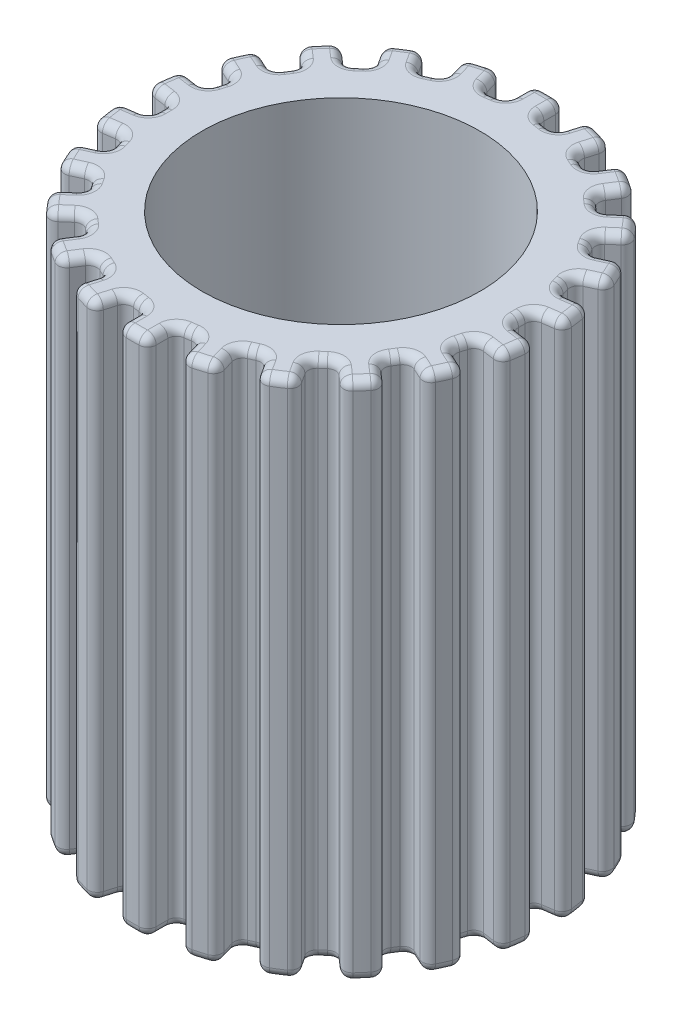
SolidWorks part; units mm, degrees
ref_plane "Front Plane" through (0, 0, 0) normal (0, 0, 1) x (1, 0, 0)
ref_plane "Top Plane" through (0, 0, 0) normal (0, 1, 0) x (1, 0, 0)
ref_plane "Right Plane" through (0, 0, 0) normal (1, 0, 0) x (0, 0, -1)
sketch "Sketch2" plane through (0, 0, 0) normal (0, 1, 0) x (1, 0, 0)
  line L0 (0, 4) -> (0, 6) construction
  line L1 (0.428, 5.9847) -> (0.428, 5.1882)
  line L2 (-0.428, 5.9847) -> (-0.428, 5.1882)
  line L3 (2.0968, 5.6217) -> (1.8724, 4.8575)
  line L4 (1.2754, 5.8629) -> (1.051, 5.0987)
  line L5 (3.5957, 4.8032) -> (3.1651, 4.1332)
  line L6 (2.8755, 5.2661) -> (2.4449, 4.596)
  line L7 (4.8032, 3.5957) -> (4.2013, 3.0741)
  line L8 (4.2426, 4.2426) -> (3.6407, 3.7211)
  line L9 (5.6217, 2.0968) -> (4.8972, 1.7659)
  line L10 (5.2661, 2.8755) -> (4.5416, 2.5446)
  line L11 (5.9847, 0.428) -> (5.1963, 0.3147)
  line L12 (5.8629, 1.2754) -> (5.0745, 1.162)
  line L13 (5.8629, -1.2754) -> (5.0745, -1.162)
  line L14 (5.9847, -0.428) -> (5.1963, -0.3147)
  line L15 (5.2661, -2.8755) -> (4.5416, -2.5446)
  line L16 (5.6217, -2.0968) -> (4.8972, -1.7659)
  line L17 (4.2426, -4.2426) -> (3.6407, -3.7211)
  line L18 (4.8032, -3.5957) -> (4.2013, -3.0741)
  line L19 (2.8755, -5.2661) -> (2.4449, -4.596)
  line L20 (3.5957, -4.8032) -> (3.1651, -4.1332)
  line L21 (1.2754, -5.8629) -> (1.051, -5.0987)
  line L22 (2.0968, -5.6217) -> (1.8724, -4.8575)
  line L23 (-0.428, -5.9847) -> (-0.428, -5.1882)
  line L24 (0.428, -5.9847) -> (0.428, -5.1882)
  line L25 (-2.0968, -5.6217) -> (-1.8724, -4.8575)
  line L26 (-1.2754, -5.8629) -> (-1.051, -5.0987)
  line L27 (-3.5957, -4.8032) -> (-3.1651, -4.1332)
  line L28 (-2.8755, -5.2661) -> (-2.4449, -4.596)
  line L29 (-4.8032, -3.5957) -> (-4.2013, -3.0741)
  line L30 (-4.2426, -4.2426) -> (-3.6407, -3.7211)
  line L31 (-5.6217, -2.0968) -> (-4.8972, -1.7659)
  line L32 (-5.2661, -2.8755) -> (-4.5416, -2.5446)
  line L33 (-5.9847, -0.428) -> (-5.1963, -0.3147)
  line L34 (-5.8629, -1.2754) -> (-5.0745, -1.162)
  line L35 (-5.8629, 1.2754) -> (-5.0745, 1.162)
  line L36 (-5.9847, 0.428) -> (-5.1963, 0.3147)
  line L37 (-5.2661, 2.8755) -> (-4.5416, 2.5446)
  line L38 (-5.6217, 2.0968) -> (-4.8972, 1.7659)
  line L39 (-4.2426, 4.2426) -> (-3.6407, 3.7211)
  line L40 (-4.8032, 3.5957) -> (-4.2013, 3.0741)
  line L41 (-2.8755, 5.2661) -> (-2.4449, 4.596)
  line L42 (-3.5957, 4.8032) -> (-3.1651, 4.1332)
  line L43 (-1.2754, 5.8629) -> (-1.051, 5.0987)
  line L44 (-2.0968, 5.6217) -> (-1.8724, 4.8575)
  circle A0 centre (0, 0) radius 4
  arc A1 (0.428, 5.9847) -> (-0.428, 5.9847) centre (0, 0) ccw
  arc A2 (2.0968, 5.6217) -> (1.2754, 5.8629) centre (0, 0) ccw
  arc A3 (3.5957, 4.8032) -> (2.8755, 5.2661) centre (0, 0) ccw
  arc A4 (4.8032, 3.5957) -> (4.2426, 4.2426) centre (0, 0) ccw
  arc A5 (5.6217, 2.0968) -> (5.2661, 2.8755) centre (0, 0) ccw
  arc A6 (5.9847, 0.428) -> (5.8629, 1.2754) centre (0, 0) ccw
  arc A7 (5.8629, -1.2754) -> (5.9847, -0.428) centre (0, 0) ccw
  arc A8 (5.2661, -2.8755) -> (5.6217, -2.0968) centre (0, 0) ccw
  arc A9 (4.2426, -4.2426) -> (4.8032, -3.5957) centre (0, 0) ccw
  arc A10 (2.8755, -5.2661) -> (3.5957, -4.8032) centre (0, 0) ccw
  arc A11 (1.2754, -5.8629) -> (2.0968, -5.6217) centre (0, 0) ccw
  arc A12 (-0.428, -5.9847) -> (0.428, -5.9847) centre (0, 0) ccw
  arc A13 (-2.0968, -5.6217) -> (-1.2754, -5.8629) centre (0, 0) ccw
  arc A14 (-3.5957, -4.8032) -> (-2.8755, -5.2661) centre (0, 0) ccw
  arc A15 (-4.8032, -3.5957) -> (-4.2426, -4.2426) centre (0, 0) ccw
  arc A16 (-5.6217, -2.0968) -> (-5.2661, -2.8755) centre (0, 0) ccw
  arc A17 (-5.9847, -0.428) -> (-5.8629, -1.2754) centre (0, 0) ccw
  arc A18 (-5.8629, 1.2754) -> (-5.9847, 0.428) centre (0, 0) ccw
  arc A19 (-5.2661, 2.8755) -> (-5.6217, 2.0968) centre (0, 0) ccw
  arc A20 (-4.2426, 4.2426) -> (-4.8032, 3.5957) centre (0, 0) ccw
  arc A21 (-2.8755, 5.2661) -> (-3.5957, 4.8032) centre (0, 0) ccw
  arc A22 (-1.2754, 5.8629) -> (-2.0968, 5.6217) centre (0, 0) ccw
  arc A23 (-0.428, 5.1882) -> (-1.051, 5.0987) centre (0, 0) ccw
  arc A24 (1.051, 5.0987) -> (0.428, 5.1882) centre (0, 0) ccw
  arc A25 (2.4449, 4.596) -> (1.8724, 4.8575) centre (0, 0) ccw
  arc A26 (3.6407, 3.7211) -> (3.1651, 4.1332) centre (0, 0) ccw
  arc A27 (4.5416, 2.5446) -> (4.2013, 3.0741) centre (0, 0) ccw
  arc A28 (5.0745, 1.162) -> (4.8972, 1.7659) centre (0, 0) ccw
  arc A29 (5.1963, -0.3147) -> (5.1963, 0.3147) centre (0, 0) ccw
  arc A30 (-1.8724, 4.8575) -> (-2.4449, 4.596) centre (0, 0) ccw
  arc A31 (-3.1651, 4.1332) -> (-3.6407, 3.7211) centre (0, 0) ccw
  arc A32 (-4.2013, 3.0741) -> (-4.5416, 2.5446) centre (0, 0) ccw
  arc A33 (-4.8972, 1.7659) -> (-5.0745, 1.162) centre (0, 0) ccw
  arc A34 (-5.1963, 0.3147) -> (-5.1963, -0.3147) centre (0, 0) ccw
  arc A35 (-5.0745, -1.162) -> (-4.8972, -1.7659) centre (0, 0) ccw
  arc A36 (-4.5416, -2.5446) -> (-4.2013, -3.0741) centre (0, 0) ccw
  arc A37 (-3.6407, -3.7211) -> (-3.1651, -4.1332) centre (0, 0) ccw
  arc A38 (-2.4449, -4.596) -> (-1.8724, -4.8575) centre (0, 0) ccw
  arc A39 (-1.051, -5.0987) -> (-0.428, -5.1882) centre (0, 0) ccw
  arc A40 (0.428, -5.1882) -> (1.051, -5.0987) centre (0, 0) ccw
  arc A41 (1.8724, -4.8575) -> (2.4449, -4.596) centre (0, 0) ccw
  arc A42 (3.1651, -4.1332) -> (3.6407, -3.7211) centre (0, 0) ccw
  arc A43 (4.2013, -3.0741) -> (4.5416, -2.5446) centre (0, 0) ccw
  arc A44 (4.8972, -1.7659) -> (5.0745, -1.162) centre (0, 0) ccw
  point P95 (0, 0)
  dimension "D1" = 8
  dimension "D2" = 12
  dimension "D3" = 22
extrude "Boss-Extrude1" add sketch "Sketch2" along normal blind 15
fillet "Fillet1" radius 0.25 47 edges at (5.2594, 15, 1.9314) (2.6602, 0, 4.9311) (0.428, 0, 5.5865) (-2.6602, 15, 4.9311) (-3.3804, 15, 4.4682) (-4.9038, 0, 2.7101) (-5.4687, 0, 1.2187) (-5.5905, 15, 0.3714) (-5.2594, 0, -1.9314) (-4.5023, 15, -3.3349) (-4.9038, 15, -2.7101) (-0.428, 15, -5.5865) (-1.1632, 0, -5.4808) (1.1632, 0, -5.4808) (1.9846, 15, -5.2396) (3.9417, 15, -3.9819) (3.3804, 0, -4.4682) (5.9389, 15, 0.8539) (5.9847, 7.5, 0.428) (4.995, 15, -1.4667) (4.3795, 15, 2.8145) (-5.2059, 0, 0) (-4.8972, 7.5, -1.7659) (-4.995, 15, -1.4667) (-4.5416, 7.5, -2.5446) (-3.1651, 7.5, -4.1332) (-3.4091, 15, -3.9343) (-2.4449, 7.5, -4.596) (-2.1626, 0, -4.7354) (1.051, 7.5, -5.0987) (0.7409, 15, -5.1529) (1.8724, 7.5, -4.8575) (2.1626, 0, -4.7354) (4.5416, 7.5, -2.5446) (5.9389, 15, -0.8539) (4.2426, 7.5, -4.2426) (3.5957, 7.5, -4.8032) (3.2438, 15, -5.0475) (-0.428, 7.5, -5.9847) (0, 0, -6) (-1.2754, 7.5, -5.8629) (-3.2438, 0, -5.0475) (-4.8032, 7.5, -3.5957) (-4.5345, 0, -3.9292) (-1.6904, 15, 5.757) (1.6904, 0, 5.757) (0.428, 7.5, 5.9847)
